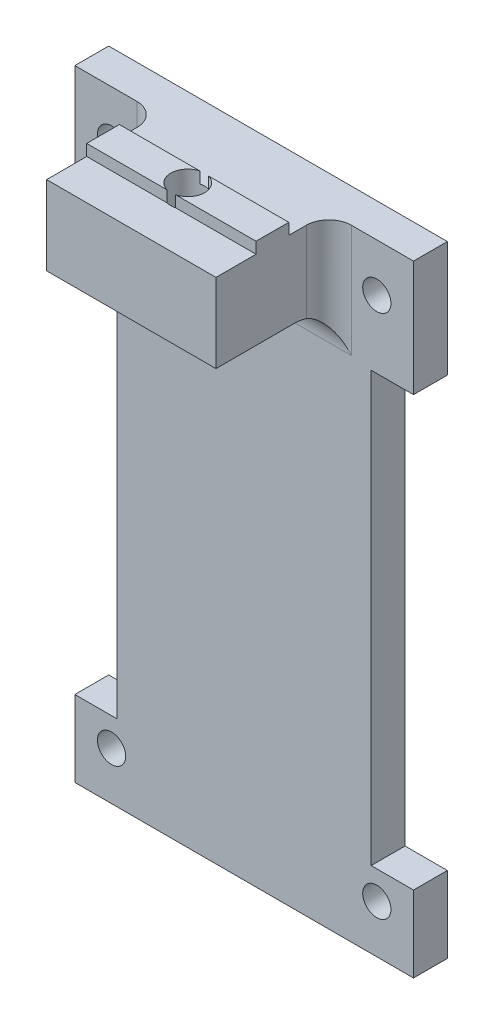
SolidWorks part; units mm, degrees
ref_plane "Front Plane" through (0, 0, 0) normal (0, 0, 1) x (1, 0, 0)
ref_plane "Top Plane" through (0, 0, 0) normal (0, 1, 0) x (1, 0, 0)
ref_plane "Right Plane" through (0, 0, 0) normal (1, 0, 0) x (0, 0, -1)
sketch "Sketch1" plane through (0, 0, 0) normal (0, 0, 1) x (1, 0, 0)
  line L0 (-15, 55) -> (-15, 44.75)
  line L1 (-15, 44.75) -> (-11.25, 44.75)
  line L2 (-11.25, 44.75) -> (-11.25, 6.75)
  line L3 (-11.25, 6.75) -> (-15, 6.75)
  line L4 (-15, 6.75) -> (-15, 0)
  line L5 (-15, 0) -> (15, 0)
  line L6 (15, 0) -> (15, 6.75)
  line L7 (15, 6.75) -> (11.25, 6.75)
  line L8 (11.25, 6.75) -> (11.25, 44.75)
  line L9 (11.25, 44.75) -> (15, 44.75)
  line L10 (15, 44.75) -> (15, 55)
  line L11 (15, 55) -> (-15, 55)
  circle A0 centre (-11.75, 50.75) radius 1.25
  circle A1 centre (11.75, 50.75) radius 1.25
  circle A2 centre (11.75, 4.25) radius 1.25
  circle A3 centre (-11.75, 4.25) radius 1.25
  point P6 (0, 0)
  point P13 (0, -17.0144)
  point P23 (0, 0)
  point P24 (-7.6869, 7.8178)
  point P25 (0, 0)
  point P26 (0, 0)
  point P27 (-11.5744, 52.3279)
  point P28 (-15, 37.3903)
  point P29 (0, 0)
  point P30 (-8.8024, 43.3435)
  point P31 (0, 0)
  point P32 (0, 0)
  point P33 (-10.6819, 4.25)
  point P34 (0, 0)
  point P35 (-10.322, 4.25)
  point P36 (0, 0)
  dimension "D7" = 2.5
  dimension "D1" = 30
  dimension "D2" = 55
  dimension "D3" = 23.5
  dimension "D4" = 3.25
  dimension "D5" = 46.5
  dimension "D6" = 4.25
  dimension "D8" = 22.5
  dimension "D9" = 38
  dimension "D10" = 2.5
extrude "Main" add sketch "Sketch1" along normal blind 3
sketch "Sketch2" plane through (0, 0, 0) normal (1, 0, 0) x (0, 0, -1)
  line L0 (-13, 55) -> (-9.45, 55)
  line L1 (-3, 55) -> (-3, 48)
  line L2 (-3, 48) -> (-13, 48)
  line L3 (-13, 48) -> (-13, 55)
  line L4 (-9.45, 55) -> (-9.45, 56)
  line L5 (-9.45, 56) -> (-6.55, 56)
  line L6 (-6.55, 56) -> (-6.55, 55)
  line L7 (-6.55, 55) -> (-3, 55)
  line L8 (-3, 44.75) -> (-3, 55) construction
  line L9 (-3, 55) -> (0, 55) construction
  line L10 (-3, 55) -> (-3, 44.75) construction
  point P0 (-5, 55)
  dimension "D1" = 2.9
  dimension "D2" = 1
  dimension "D3" = 3.55
  dimension "D4" = 7
  dimension "D5" = 10
extrude "MakerBeamSupport" add sketch "Sketch2" along normal mid plane 15
fillet "Fillet1" radius 3 1 edges at (0, 48, 3)
fillet "Fillet2" radius 2 2 edges at (7.5, 50, 3) (-7.5, 50, 3)
sketch "Sketch3" plane through (0, 56, 0) normal (0, 1, 0) x (1, 0, 0)
  line L0 (7.5, -13) -> (-7.5, -13) construction
  circle A0 centre (0, -8) radius 1.5
  dimension "D1" = 3
  dimension "D2" = 5
extrude "Cut-Extrude1" cut sketch "Sketch3" against normal through all
